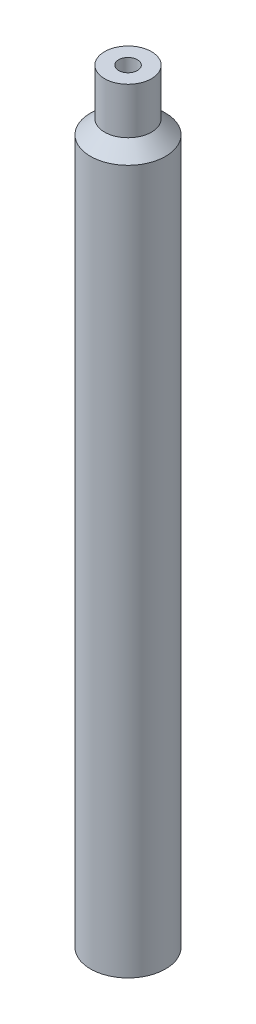
SolidWorks part; units mm, degrees
ref_plane "Спереди" through (0, 0, 0) normal (0, 0, 1) x (1, 0, 0)
ref_plane "Сверху" through (0, 0, 0) normal (0, 1, 0) x (1, 0, 0)
ref_plane "Справа" through (0, 0, 0) normal (1, 0, 0) x (0, 0, -1)
sketch "Эскиз1" plane through (0, 0, 0) normal (1, 0, 0) x (0, 0, -1)
  line L0 (5, 150) -> (2, 152.9633)
  line L1 (5, 0) -> (8, 0)
  line L2 (5, 0) -> (5, 150)
  line L3 (2, 152.9633) -> (2, 162.8371)
  line L4 (8, 0) -> (8, 150)
  line L5 (2, 162.8371) -> (5, 162.8371)
  line L6 (5, 162.8371) -> (5, 152.9633)
  line L7 (5, 152.9633) -> (8, 150)
  line L8 (0, -19.3548) -> (0, 237.0252) construction
revolve "Повернуть1" add sketch "Эскиз1" angle 360 about L8
